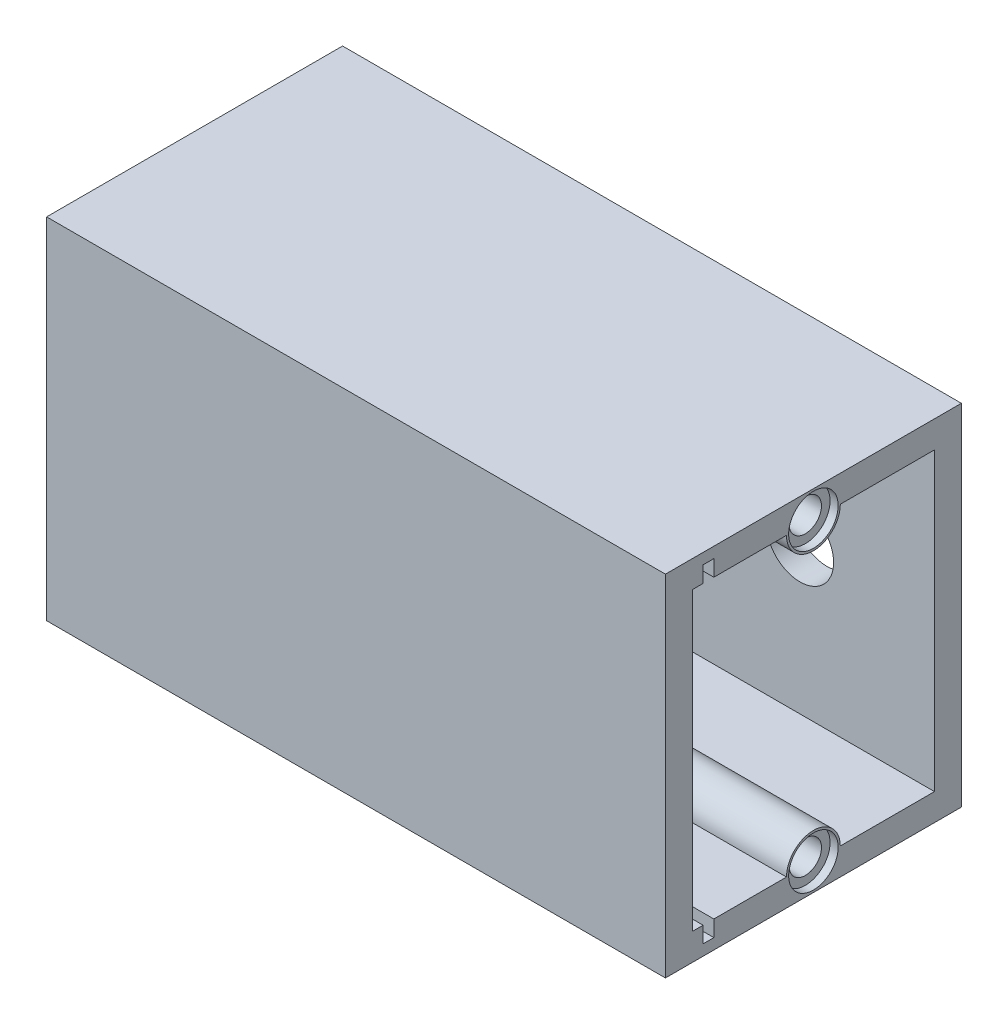
SolidWorks part; units mm, degrees
ref_plane "Plan de face" through (0, 0, 0) normal (0, 0, 1) x (1, 0, 0)
ref_plane "Plan de dessus" through (0, 0, 0) normal (0, 1, 0) x (1, 0, 0)
ref_plane "Plan de droite" through (0, 0, 0) normal (1, 0, 0) x (0, 0, -1)
sketch "Esquisse1" plane through (0, 0, 0) normal (0, 0, 1) x (1, 0, 0)
  line L0 (0, 32.5) -> (120, 32.5) construction
  line L1 (0, 0) -> (120, 0)
  line L2 (0, 0) -> (0, 65)
  line L3 (0, 65) -> (120, 65)
  line L4 (120, 0) -> (120, 65)
  line L5 (60, 65) -> (60, 0) construction
  line L6 (60, 32.5) -> (0, 32.5) construction
  line L7 (0, 32.5) -> (30, 32.5) construction
  line L8 (30, 32.5) -> (30, 65) construction
  line L9 (30, 65) -> (30, 0) construction
  line L10 (30, 0) -> (60, 0) construction
  line L11 (60, 0) -> (120, 0) construction
  line L12 (90, 0) -> (90, 65) construction
  circle A0 centre (30, 32.5) radius 6.25
  circle A1 centre (90, 32.5) radius 6.25
  dimension "D3" = 12.5
  dimension "D4" = 12.5
  dimension "D1" = 120
  dimension "D2" = 65
extrude "Boss.-Extru.1" add sketch "Esquisse1" along normal blind 5
sketch "Esquisse2" plane through (0, 0, 5) normal (0, 0, 1) x (1, 0, 0)
  line L0 (0, 65) -> (5, 65) construction
  line L1 (120, 65) -> (0, 65) construction
  line L2 (0, 65) -> (0, 60) construction
  line L3 (0, 65) -> (0, 0) construction
  line L4 (0, 60) -> (120, 60) construction
  line L5 (120, 0) -> (120, 65) construction
  line L6 (5, 65) -> (5, 0) construction
  line L7 (0, 0) -> (120, 0) construction
  line L8 (120, 0) -> (120, 5) construction
  line L9 (120, 0) -> (115, 0) construction
  line L10 (115, 0) -> (115, 65) construction
  line L11 (120, 5) -> (0, 5) construction
  line L12 (5, 60) -> (115, 60)
  line L13 (115, 60) -> (115, 5)
  line L14 (115, 5) -> (5, 5)
  line L15 (5, 5) -> (5, 60)
  line L17 (0, 65) -> (120, 65)
  line L18 (0, 65) -> (0, 0)
  line L19 (0, 0) -> (120, 0)
  line L20 (120, 65) -> (120, 0)
  line L21 (5, 60) -> (115, 60)
  line L22 (5, 60) -> (5, 5)
  line L23 (5, 5) -> (115, 5)
  line L24 (115, 60) -> (115, 5)
  line L25 (120, 0) -> (0, 0)
  line L26 (120, 0) -> (120, 65)
  line L27 (120, 65) -> (0, 65)
  line L28 (0, 0) -> (0, 65)
  line M13 (0, 65) -> (0, 0)
  line M14 (0, 0) -> (120, 0)
  line M15 (120, 0) -> (120, 65)
  line M16 (120, 65) -> (0, 65)
  dimension "D1" = 5
  dimension "D2" = 5
  dimension "D3" = 5
  dimension "D4" = 5
extrude "Boss.-Extru.3" add sketch "Esquisse2" along normal blind 45 contours L14 L15 L12 L13 M16 M13 M14 M15
sketch "Esquisse4" plane through (0, 0, 50) normal (0, 0, 1) x (1, 0, 0)
  line L1 (0, 65) -> (120, 65)
  line L2 (0, 65) -> (0, 0)
  line L3 (0, 0) -> (120, 0)
  line L4 (120, 65) -> (120, 0)
extrude "Boss.-Extru.4" add sketch "Esquisse4" along normal blind 5
sketch "Esquisse5" plane through (120, 0, 0) normal (1, 0, 0) x (0, 0, -1)
  line L1 (-55, 65) -> (0, 65)
  line L2 (-55, 65) -> (-55, 0)
  line L3 (-55, 0) -> (0, 0)
  line L4 (0, 65) -> (0, 0)
extrude "Enlèv. mat.-Extru.1" cut sketch "Esquisse5" against normal blind 5
sketch "Esquisse6" plane through (115, 0, 0) normal (1, 0, 0) x (0, 0, -1)
  line L0 (0, 65) -> (-55, 65) construction
  line L1 (-48, 63) -> (-46, 63)
  line L2 (-48, 63) -> (-48, 2)
  line L3 (-48, 2) -> (-46, 2)
  line L4 (-46, 63) -> (-46, 2)
  line L5 (-55, 0) -> (0, 0) construction
  line L6 (-50, 60) -> (-50, 5) construction
  dimension "D1" = 2
  dimension "D2" = 2
  dimension "D3" = 2
  dimension "D4" = 2
extrude "Enlèv. mat.-Extru.2" cut sketch "Esquisse6" against normal blind 62.25
sketch "Esquisse7" plane through (115, 0, 0) normal (1, 0, 0) x (0, 0, -1)
  line L0 (0, 65) -> (-55, 65) construction
  line L1 (-55, 65) -> (-27.5, 65) construction
  line L2 (-27.5, 65) -> (-27.5, 0) construction
  line L3 (-55, 0) -> (0, 0) construction
  line L4 (-46, 60) -> (-5, 60) construction
  line L5 (-50, 60) -> (-5, 60) construction
  line L6 (0, 32.5) -> (-55, 32.5) construction
  line L7 (0, 0) -> (0, 65) construction
  line L8 (-55, 65) -> (-55, 0) construction
  line L9 (-22.5, 60) -> (-32.5, 60)
  line L10 (-32.5, 5) -> (-22.5, 5)
  arc A0 (-22.5, 60) -> (-32.5, 60) centre (-27.5, 60) cw
  arc A1 (-22.5, 5) -> (-32.5, 5) centre (-27.5, 5) ccw
  dimension "D1" = 5
extrude "Boss.-Extru.6" add sketch "Esquisse7" against normal up to surface (110 mm away) contours L9 A0 | L10 A1 up to face at (5, 32.5, 27.5)
sketch "Esquisse8" plane through (115, 0, 0) normal (1, 0, 0) x (0, 0, -1)
  line L0 (-5, 60) -> (-50, 60) construction
  line L1 (-50, 60) -> (-50, 5) construction
  line L2 (-50, 5) -> (-5, 5) construction
  line L3 (-5, 5) -> (-5, 60) construction
  line L4 (-5, 60) -> (-27.5, 60) construction
  line L5 (-27.5, 60) -> (-27.5, 5) construction
  circle A0 centre (-27.5, 60) radius 3
  circle A1 centre (-27.5, 5) radius 3
  dimension "D1" = 6
  dimension "D2" = 6
extrude "Enlèv. mat.-Extru.3" cut sketch "Esquisse8" against normal blind 12
sketch "Esquisse9" plane through (115, 0, 0) normal (1, 0, 0) x (0, 0, -1)
  circle A0 centre (-27.5, 60) radius 4.6
  circle A1 centre (-27.5, 5) radius 4.6
  dimension "D1" = 9.2
  dimension "D2" = 9.2
extrude "Enlèv. mat.-Extru.7" cut sketch "Esquisse9" against normal blind 1.5
